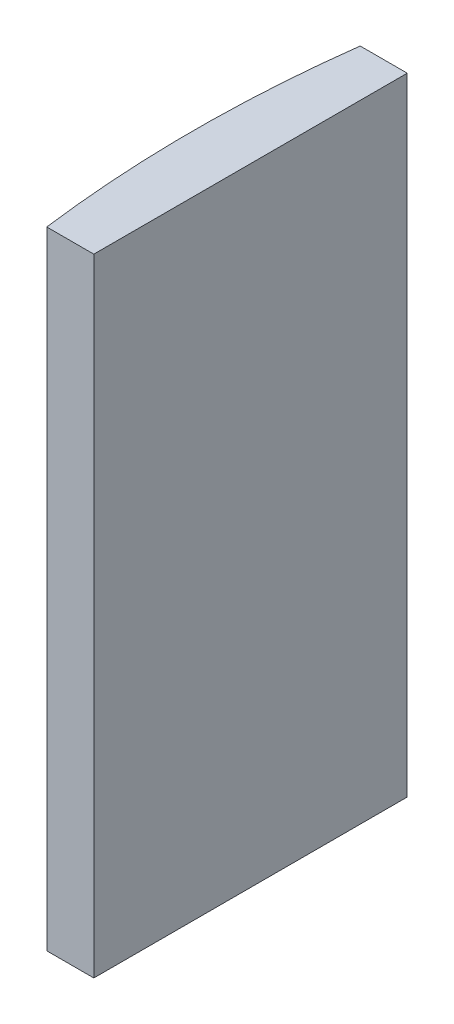
SolidWorks part; units mm, degrees
ref_plane "前视基准面" through (0, 0, 0) normal (0, 0, 1) x (1, 0, 0)
ref_plane "上视基准面" through (0, 0, 0) normal (0, 1, 0) x (1, 0, 0)
ref_plane "右视基准面" through (0, 0, 0) normal (1, 0, 0) x (0, 0, -1)
sketch "草图1" plane through (0, 0, 0) normal (0, 1, 0) x (1, 0, 0)
  line L0 (10.7432, 0) -> (-607.0701, 0) construction
  line L1 (-72.5473, 10) -> (-69.5448, 10)
  line L2 (-72.5473, -10) -> (-69.5448, -10)
  line L3 (-69.5448, 10) -> (-69.5448, -10)
  arc A0 (-72.5473, 10) -> (-72.5473, -10) centre (4.3552, 0) ccw
  point P19 (-73.1948, 0)
  point P20 (-69.5448, 0)
  dimension "D2" = 10
  dimension "D3" = 77.55
  dimension "D4" = 3.65
  dimension "D1" = 10
extrude "凸台-拉伸1" add sketch "草图1" along normal blind 40
